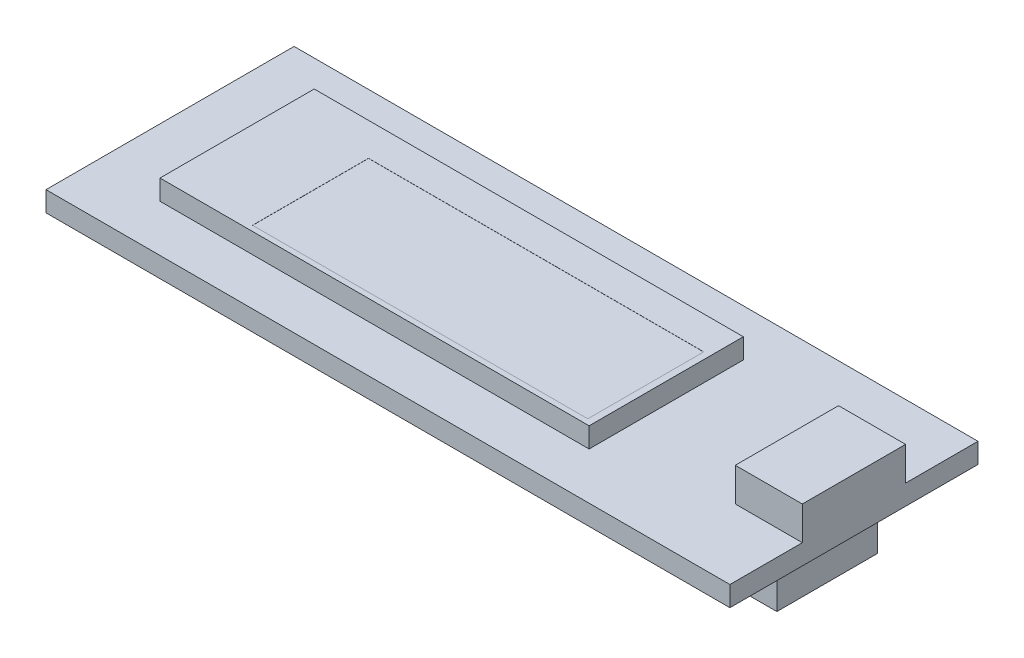
SolidWorks part; units mm, degrees
ref_plane "Front Plane" through (0, 0, 0) normal (0, 0, 1) x (1, 0, 0)
ref_plane "Top Plane" through (0, 0, 0) normal (0, 1, 0) x (1, 0, 0)
ref_plane "Right Plane" through (0, 0, 0) normal (1, 0, 0) x (0, 0, -1)
sketch "Sketch1" plane through (0, 0, 27) normal (0, 1, 0) x (1, 0, 0)
  line L2 (0, 36.25) -> (51, 36.25)
  line L3 (0, 36.25) -> (0, 17.75)
  line L4 (0, 17.75) -> (51, 17.75)
  line L5 (51, 36.25) -> (51, 17.75)
  point P0 (0, 27)
  dimension "D1" = 51
  dimension "D2" = 18.5
extrude "Boss-Extrude1" add sketch "Sketch1" along normal blind 1.5 contours L3 L4 L5 L2
sketch "Sketch2" plane through (0, 1.5, 0) normal (0, 1, 0) x (1, 0, 0)
  line L0 (51, 9.25) -> (51, -9.25) construction
  line L1 (5, 5.75) -> (37, 5.75)
  line L2 (5, 5.75) -> (5, -5.75)
  line L3 (5, -5.75) -> (37, -5.75)
  line L4 (37, 5.75) -> (37, -5.75)
  line L5 (0, -9.25) -> (51, -9.25) construction
  dimension "D1" = 14
  dimension "D2" = 32
  dimension "D3" = 11.5
  dimension "D4" = 3.5
extrude "Boss-Extrude2" add sketch "Sketch2" along normal blind 1.5
sketch "Sketch3" plane through (0, 1.5, 0) normal (0, 1, 0) x (1, 0, 0)
  line L0 (51, 9.25) -> (51, -9.25) construction
  line L1 (51, 3.85) -> (46, 3.85)
  line L2 (51, 3.85) -> (51, -3.85)
  line L3 (51, -3.85) -> (46, -3.85)
  line L4 (46, 3.85) -> (46, -3.85)
  point P6 (46, 0)
  point P7 (51, 0)
  dimension "D1" = 7.7
  dimension "D2" = 5
extrude "Boss-Extrude3" add sketch "Sketch3" along normal blind 2.5
sketch "Sketch4" plane through (0, 0, 0) normal (0, -1, 0) x (1, 0, 0)
  line L0 (51, -9.25) -> (51, 9.25) construction
  line L1 (44.7, 3.75) -> (49, 3.75)
  line L2 (44.7, 3.75) -> (44.7, -3.75)
  line L3 (44.7, -3.75) -> (49, -3.75)
  line L4 (49, 3.75) -> (49, -3.75)
  point P4 (49, 0)
  point P7 (51, 0)
  dimension "D1" = 2
  dimension "D2" = 4.3
  dimension "D3" = 7.5
extrude "Boss-Extrude4" add sketch "Sketch4" along normal blind 4
sketch "Sketch5" plane through (0, 3, 0) normal (0, 1, 0) x (1, 0, 0)
  line L1 (36.5, -5.35) -> (11.5, -5.35)
  line L2 (36.5, -5.35) -> (36.5, 3.3)
  line L3 (36.5, 3.3) -> (11.5, 3.3)
  line L4 (11.5, -5.35) -> (11.5, 3.3)
  line L5 (37, -5.75) -> (37, 5.75) construction
  line L6 (5, -5.75) -> (37, -5.75) construction
  dimension "D1" = 0.5
  dimension "D2" = 25
  dimension "D3" = 0.4
  dimension "D4" = 8.65
extrude "Cut-Extrude1" cut sketch "Sketch5" against normal blind 0.01
